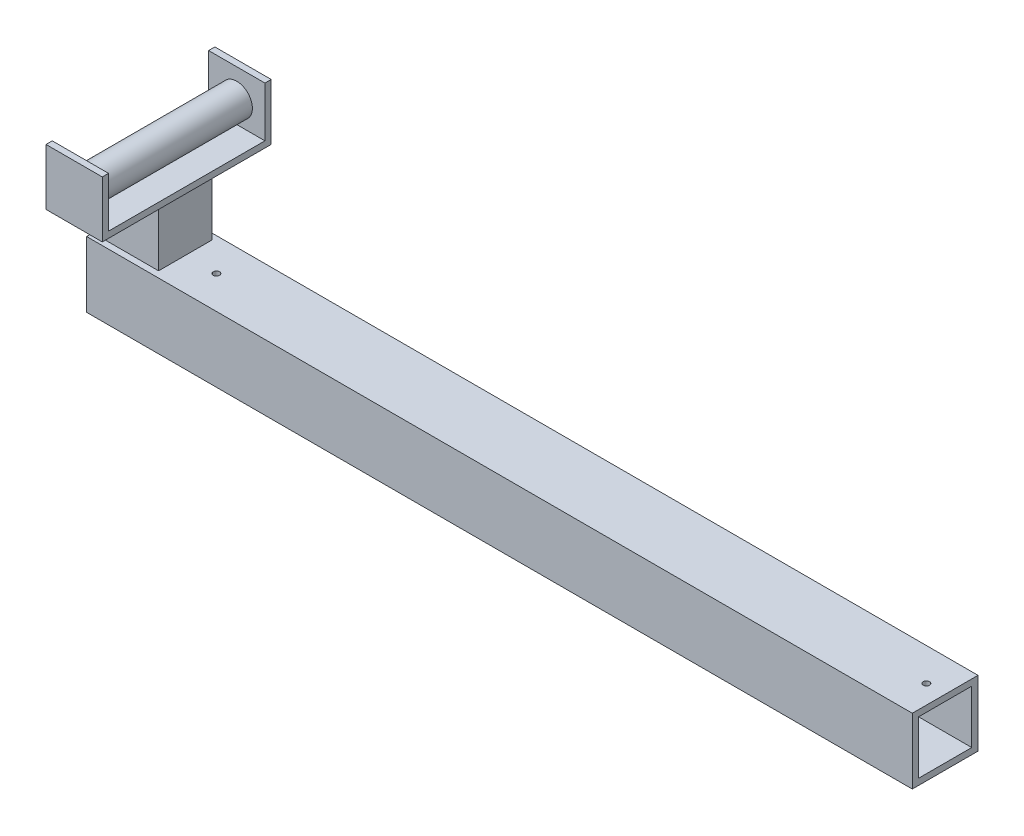
SolidWorks part; units mm, degrees
ref_plane "Front Plane" through (0, 0, 0) normal (0, 0, 1) x (1, 0, 0)
ref_plane "Top Plane" through (0, 0, 0) normal (0, 1, 0) x (1, 0, 0)
ref_plane "Right Plane" through (0, 0, 0) normal (1, 0, 0) x (0, 0, -1)
sketch "Sketch1" plane through (0, 0, 0) normal (0, 0, 1) x (1, 0, 0)
  line L3 (0, 0) -> (1676.4, 0)
  line L4 (0, 0) -> (0, 133.35)
  line L5 (0, 133.35) -> (1676.4, 133.35)
  line L6 (1676.4, 0) -> (1676.4, 133.35)
  dimension "D1" = 1676.4
  dimension "D2" = 133.35
extrude "Boss-Extrude1" add sketch "Sketch1" along normal blind 133.35 contours L5 L6 L3 L4
sketch "Sketch2" plane through (1676.4, 0, 0) normal (1, 0, 0) x (0, 0, -1)
  line L0 (-133.35, 0) -> (0, 0) construction
  line L1 (-120.65, 12.7) -> (-12.7, 12.7)
  line L2 (-120.65, 12.7) -> (-120.65, 120.65)
  line L3 (-120.65, 120.65) -> (-12.7, 120.65)
  line L4 (-12.7, 12.7) -> (-12.7, 120.65)
  line L5 (0, 0) -> (0, 133.35) construction
  dimension "D1" = 107.95
  dimension "D2" = 107.95
  dimension "D3" = 12.7
  dimension "D4" = 12.7
extrude "Cut-Extrude1" cut sketch "Sketch2" against normal blind 1524 contours L3 L4 L1 L2
sketch "Sketch3" plane through (0, 133.35, 0) normal (0, 1, 0) x (1, 0, 0)
  line L0 (0, 0) -> (1676.4, 0) construction
  line L1 (25.4, -12.7) -> (133.35, -12.7)
  line L2 (25.4, -12.7) -> (25.4, -120.65)
  line L3 (25.4, -120.65) -> (133.35, -120.65)
  line L4 (133.35, -12.7) -> (133.35, -120.65)
  line L5 (0, -133.35) -> (0, 0) construction
  dimension "D1" = 107.95
  dimension "D2" = 107.95
  dimension "D3" = 12.7
  dimension "D4" = 25.4
extrude "Boss-Extrude2" add sketch "Sketch3" along normal blind 114.3
sketch "Sketch4" plane through (0, 247.65, 0) normal (0, 1, 0) x (1, 0, 0)
  line L0 (25.4, -12.7) -> (25.4, -120.65) construction
  line L9 (25.4, -241.3) -> (139.7, -241.3)
  line L10 (25.4, -241.3) -> (25.4, 101.6)
  line L11 (25.4, 101.6) -> (139.7, 101.6)
  line L12 (139.7, -241.3) -> (139.7, 101.6)
  line L13 (133.35, -12.7) -> (25.4, -12.7) construction
  dimension "D1" = 342.9
  dimension "D2" = 0
  dimension "D3" = 114.3
  dimension "D4" = 114.3
extrude "Boss-Extrude3" add sketch "Sketch4" along normal blind 12.7
sketch "Sketch5" plane through (0, 260.35, 0) normal (0, 1, 0) x (1, 0, 0)
  line L0 (139.7, -241.3) -> (139.7, 101.6) construction
  line L1 (25.4, 101.6) -> (139.7, 101.6)
  line L2 (25.4, 101.6) -> (25.4, 88.9)
  line L3 (25.4, 88.9) -> (139.7, 88.9)
  line L4 (139.7, 101.6) -> (139.7, 88.9)
  line L6 (25.4, -241.3) -> (139.7, -241.3)
  line L7 (25.4, -241.3) -> (25.4, -228.6)
  line L8 (25.4, -228.6) -> (139.7, -228.6)
  line L9 (139.7, -241.3) -> (139.7, -228.6)
  dimension "D1" = 12.7
  dimension "D2" = 12.7
extrude "Boss-Extrude4" add sketch "Sketch5" along normal blind 101.6
sketch "Sketch6" plane through (0, 0, -88.9) normal (0, 0, 1) x (1, 0, 0)
  line L0 (25.4, 361.95) -> (139.7, 361.95) construction
  line L1 (25.4, 361.95) -> (25.4, 247.65) construction
  circle A0 centre (82.55, 304.8) radius 31.75
  dimension "D1" = 63.5
  dimension "D2" = 57.15
  dimension "D3" = 57.15
extrude "Boss-Extrude5" add sketch "Sketch6" along normal up to surface (317.5 mm away) up to face at (82.55, 311.15, 228.6)
sketch "Sketch7" plane through (0, 133.35, 0) normal (0, 1, 0) x (1, 0, 0)
  line L0 (133.35, -120.65) -> (133.35, -12.7) construction
  line L1 (0, -133.35) -> (1676.4, -133.35) construction
  line L3 (1676.4, -133.35) -> (1676.4, 0) construction
  line L4 (0, 0) -> (1676.4, 0) construction
  circle A0 centre (196.85, -66.675) radius 6.35
  circle A1 centre (1638.3, -66.675) radius 6.35
  dimension "D1" = 12.7
  dimension "D4" = 12.7
  dimension "D6" = 66.675
  dimension "D2" = 63.5
  dimension "D3" = 66.675
  dimension "D5" = 38.1
extrude "Cut-Extrude2" cut sketch "Sketch7" against normal up to surface (12.7 mm away) up to face at (914.4, 120.65, 66.675)
